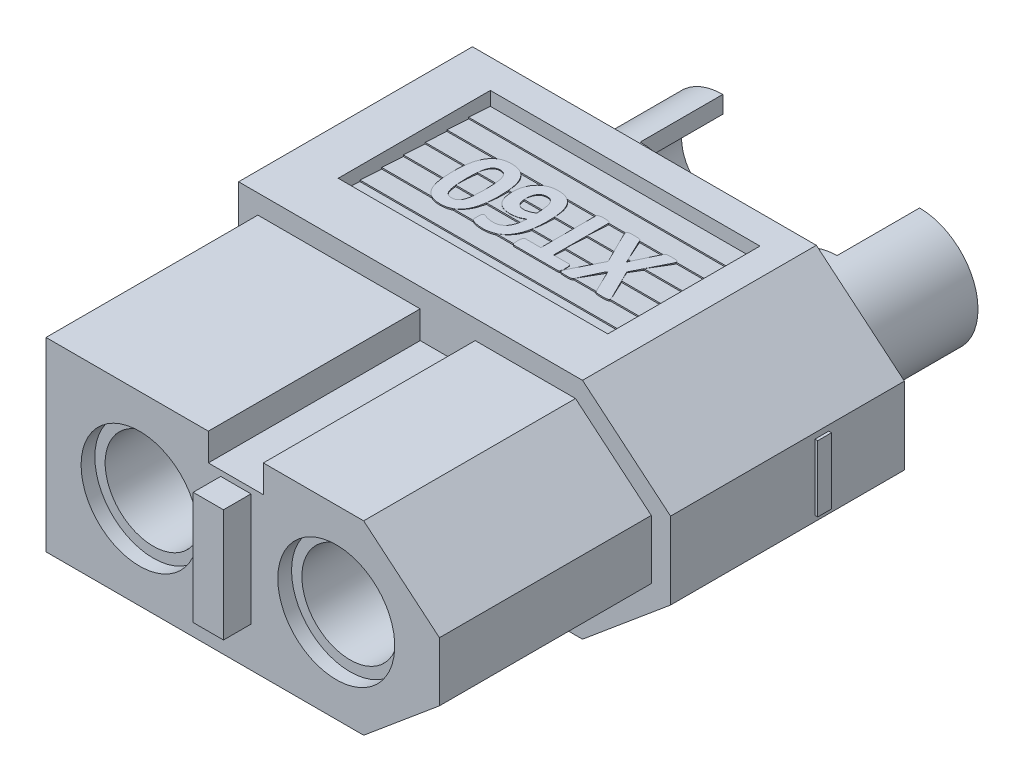
SolidWorks part; units mm, degrees
material "Náilon 101"
ref_plane "Plano frontal" through (0, 0, 0) normal (0, 0, 1) x (1, 0, 0)
ref_plane "Plano superior" through (0, 0, 0) normal (0, 1, 0) x (1, 0, 0)
ref_plane "Plano direito" through (0, 0, 0) normal (1, 0, 0) x (0, 0, -1)
sketch "Esboço1" plane through (0, 0, 0) normal (0, 0, 1) x (1, 0, 0)
  line L0 (0, 0) -> (0, 4.075)
  line L1 (0, 4.075) -> (12.5, 4.075)
  line L2 (12.5, 4.075) -> (15.7, 1.4)
  line L3 (15.7, 1.4) -> (15.7, -1.4)
  line L4 (15.7, 0) -> (0, 0) construction
  line L5 (12.5, -4.075) -> (15.7, -1.4)
  line L6 (0, -4.075) -> (12.5, -4.075)
  line L7 (0, 0) -> (0, -4.075)
  dimension "D1" = 8.15
  dimension "D2" = 12.5
  dimension "D3" = 15.7
  dimension "D4" = 2.8
extrude "Ressalto-extrusão1" add sketch "Esboço1" against normal blind 16.2
sketch "Esboço2" plane through (0, 0, 0) normal (0, 0, 1) x (1, 0, 0)
  line L12 (0.7, 3.375) -> (0.7, -3.375)
  line L13 (0.7, -3.375) -> (12.246, -3.375)
  line L14 (12.246, -3.375) -> (15, -1.0728)
  line L15 (15, -1.0728) -> (15, 1.0728)
  line L16 (15, 1.0728) -> (12.246, 3.375)
  line L17 (12.246, 3.375) -> (0.7, 3.375)
  line L18 (0.7, 3.375) -> (0.7, -3.375)
  line L19 (0.7, -3.375) -> (12.246, -3.375)
  line L20 (12.246, -3.375) -> (15, -1.0728)
  line L21 (15, -1.0728) -> (15, 1.0728)
  line L22 (15, 1.0728) -> (12.246, 3.375)
  line L23 (12.246, 3.375) -> (0.7, 3.375)
  dimension "D1" = 0.7
sketch "Esboço3" plane through (15.7, 0, 0) normal (1, 0, 0) x (0, 0, -1)
  line L0 (13.2, 0) -> (16.2, 0) construction
  line L1 (12.95, -1.2) -> (13.45, -1.2)
  line L2 (12.95, -1.2) -> (12.95, 1.2)
  line L3 (12.95, 1.2) -> (13.45, 1.2)
  line L4 (13.45, -1.2) -> (13.45, 1.2)
  line L5 (12.95, -1.2) -> (13.45, 1.2) construction
  line L6 (12.95, 1.2) -> (13.45, -1.2) construction
  line L7 (16.2, -1.4) -> (16.2, 1.4) construction
  point P0 (13.2, 0)
  dimension "D1" = 0.5
  dimension "D2" = 2.4
  dimension "D3" = 3
extrude "Ressalto-extrusão2" add sketch "Esboço3" along normal blind 0.1 and the other way offset from surface (15.8 mm away) 0.1 other way up to face at (0, 0, -8.1)
sketch "Esboço4" plane through (0, 0, 0) normal (-1, 0, 0) x (0, 0, 1)
  line L0 (-13.45, 0) -> (-12.95, 0) construction
  line L1 (-13.45, -1.2) -> (-13.45, 1.2) construction
  line L2 (-12.95, 1.2) -> (-12.95, -1.2) construction
  line L3 (-12.95, 1.2) -> (-13.45, 1.2) construction
  line L4 (-14.4, -0.25) -> (-12, -0.25)
  line L5 (-14.4, -0.25) -> (-14.4, 0.25)
  line L6 (-14.4, 0.25) -> (-12, 0.25)
  line L7 (-12, -0.25) -> (-12, 0.25)
  line L8 (-14.4, -0.25) -> (-12, 0.25) construction
  line L9 (-14.4, 0.25) -> (-12, -0.25) construction
  point P6 (-13.2, 0)
extrude "Ressalto-extrusão3" add sketch "Esboço4" along normal up to surface (0.1 mm away) up to face at (-0.1, 0, -13.2)
sketch "Esboço5" plane through (0, 0, -16.2) normal (0, 0, -1) x (-1, 0, 0)
  line L0 (-15.7, 0) -> (-11.25, 0) construction
  line L1 (-15.7, -1.4) -> (-15.7, 1.4) construction
  line L2 (-11.25, 0) -> (-4.1, 0) construction
  line L3 (-4.1, 0) -> (0, 0) construction
  line L4 (0, 0.25) -> (0, -0.25) construction
  circle A0 centre (-4.1, 0) radius 2.925
  circle A1 centre (-11.25, 0) radius 2.925
  dimension "D1" = 5.85
  dimension "D2" = 7.15
  dimension "D3" = 4.1
extrude "Corte-extrusão2" cut sketch "Esboço5" against normal blind 3.5
sketch "Esboço6" plane through (0, 0, -12.7) normal (0, 0, -1) x (-1, 0, 0)
  circle A2 centre (-11.25, 0) radius 2.125
  circle A3 centre (-4.1, 0) radius 2.125
  dimension "D1" = 4.25
extrude "Corte-extrusão3" cut sketch "Esboço6" against normal through all
sketch "Esboço7" plane through (0, 0, -16.2) normal (0, 0, -1) x (-1, 0, 0)
  circle A0 centre (-11.25, 0) radius 2.125 construction
  circle A1 centre (-4.1, 0) radius 2.125 construction
  circle A2 centre (-11.25, 0) radius 2.125
  circle A3 centre (-4.1, 0) radius 2.125
extrude "Ressalto-extrusão4" add sketch "Esboço7" along normal blind 5 and the other way offset from surface (15.7 mm away) 0.5 other way up to face at (9.125, 0, 0)
hole_wizard "Furo de diâmetro Ø3.0 (3)1" positions "Esboço9" profile "Esboço8" hole size "Ø3.0" standard "Métrico Ansi"
sketch "Esboço9" plane through (0, 0, -21.2) normal (0, 0, -1) x (-1, 0, 0)
  point P0 (-11.25, 0)
  point P1 (-4.1, 0)
sketch "Esboço8" plane through (11.25, 0, -21.2) normal (1, 0, 0) x (0, 1, 0)
  line L0 (0, 0) -> (0, 4.5013)
  line L1 (0, 4.5013) -> (1.5, 3.6)
  line L2 (1.5, 3.6) -> (1.5, 0)
  line L5 (1.5, 0) -> (0, 0)
  line L10 (0, 4.5013) -> (-1.5, 3.6) construction
  line L11 (0, -6.35) -> (0, 107.95) construction
  dimension "Hole Dia." = 3
  dimension "Hole Depth" = 3.6
  dimension "Drill Angle" = 118
sketch "Esboço10" plane through (0, 4.075, 0) normal (0, 1, 0) x (1, 0, 0)
  line L0 (4.1, 21.2) -> (11.25, 21.2) construction
  line L1 (5.6, 21.2) -> (2.6, 21.2) construction
  line L2 (13.375, 21.2) -> (9.125, 21.2) construction
  line L3 (7.675, 21.2) -> (7.675, 16.2) construction
  line L4 (12.5, 16.2) -> (0, 16.2) construction
  line L5 (6.225, 12.7) -> (6.225, 21.2) construction
  line L6 (4.1, 21.2) -> (6.225, 21.2)
  line L7 (4.1, 21.2) -> (4.1, 18.2)
  line L8 (4.1, 18.2) -> (6.225, 18.2)
  line L9 (6.225, 21.2) -> (6.225, 18.2)
  line L10 (9.125, 21.2) -> (9.125, 18.2)
  line L11 (11.25, 18.2) -> (9.125, 18.2)
  line L12 (11.25, 21.2) -> (11.25, 18.2)
  line L13 (11.25, 21.2) -> (9.125, 21.2)
  dimension "D1" = 3
extrude "Corte-extrusão4" cut sketch "Esboço10" against normal through all
sketch "Esboço12" plane through (0, 0, 0) normal (-1, 0, 0) x (0, 0, 1)
  line L0 (-15.15, 4.075) -> (-15.15, 3.575)
  line L1 (-16.2, 4.075) -> (0, 4.075) construction
  line L2 (-15.15, 3.575) -> (-14.36, 3.625)
  line L3 (-14.36, 3.625) -> (-14.36, 3.575)
  line L4 (-15.15, 3.575) -> (-9.62, 3.575) construction
  line L5 (-16.2, 4.075) -> (-16.2, -4.075) construction
  line L6 (-14.36, 3.575) -> (-13.57, 3.625)
  line L7 (-13.57, 3.625) -> (-13.57, 3.575)
  line L8 (-13.57, 3.575) -> (-12.78, 3.625)
  line L9 (-12.78, 3.625) -> (-12.78, 3.575)
  line L10 (-12.78, 3.575) -> (-11.99, 3.625)
  line L11 (-11.99, 3.625) -> (-11.99, 3.575)
  line L12 (-11.99, 3.575) -> (-11.2, 3.625)
  line L13 (-11.2, 3.625) -> (-11.2, 3.575)
  line L14 (-11.2, 3.575) -> (-10.41, 3.625)
  line L15 (-10.41, 3.625) -> (-10.41, 3.575)
  line L16 (-10.41, 3.575) -> (-9.62, 3.625)
  line L17 (-9.62, 3.625) -> (-9.62, 3.575) construction
  line L18 (-15.15, 3.575) -> (-14.36, 3.575) construction
  line L19 (-9.62, 3.625) -> (-9.62, 4.075)
  line L20 (-15.15, 4.075) -> (-9.62, 4.075)
  line L21 (-9.62, 4.075) -> (-9.6373, 4.0753)
  line M2 (0, 4.075) -> (-16.2, 4.075)
  dimension "D1" = 0.5
  dimension "D2" = 0.79
  dimension "D3" = 0.05
  dimension "D4" = 1.05
  dimension "D6" = 0.79
  dimension "D5" = 7
extrude "Corte-extrusão5" cut sketch "Esboço12" against normal blind 9.8 from offset 1.7 contours L16 L19 L0 L2 L3 L6 L7 L8 L9 L10 L11 L12 L13 L14 L15 M2 offset against normal yes
mirror "Espelhar1" about plane through (0, 0, 0) normal (0, 1, 0) of "Corte-extrusão5"
ref_plane "Plano1" through (0, 3.575, 0) normal (0, 1, 0) x (-1, 0, 0)
sketch "Esboço13" plane through (0, 3.575, 0) normal (0, 1, 0) x (-1, 0, 0)
  line L0 (-10.1, -13.635) -> (-3.1, -13.635) construction
  line L1 (-3.1, -13.635) -> (-6.6, -13.635) construction
  line L2 (-6.6, -13.635) -> (-6.6, -15.15) construction
  line L4 (-11.5, -15.15) -> (-1.7, -15.15) construction
  line L5 (-10.1, -13.635) -> (-10.1, -11.135) construction
  line L6 (-10.1, -11.135) -> (-3.1, -11.135) construction
  line L7 (-3.1, -11.135) -> (-3.1, -13.635) construction
  line L8 (-6.6, -11.135) -> (-6.6, -9.62) construction
  line L9 (-11.5, -9.62) -> (-1.7, -9.62) construction
  text T0 "XT60" font "Calibri" height 2.5
  dimension "D1" = 7
  dimension "D2" = 2.5
extrude "Ressalto-extrusão6" add sketch "Esboço13" along normal up to vertex (0.05 mm away) up to point (11.5, 3.625, -11.2)
ref_plane "Plano2" through (0, -3.575, 0) normal (0, 1, 0) x (-1, 0, 0)
sketch "Esboço14" plane through (0, -3.575, 0) normal (0, 1, 0) x (-1, 0, 0)
  line L0 (-6.6, -9.62) -> (-6.6, -10.735) construction
  line L1 (-11.5, -9.62) -> (-1.7, -9.62) construction
  line L2 (-6.6, -10.735) -> (-2.8, -10.735) construction
  line L3 (-2.8, -10.735) -> (-2.8, -14.035) construction
  line L4 (-2.8, -14.035) -> (-10.4, -14.035) construction
  line L5 (-10.4, -14.035) -> (-10.4, -10.735) construction
  line L6 (-10.4, -10.735) -> (-6.6, -10.735) construction
  line L7 (-6.6, -14.035) -> (-6.6, -15.15) construction
  line L8 (-11.5, -15.15) -> (-1.7, -15.15) construction
  text T0 "TGY" font "Calibri" height 3.3
  dimension "D1" = 3.3
  dimension "D2" = 7.6
extrude "Ressalto-extrusão7" add sketch "Esboço14" against normal up to vertex (0.05 mm away) up to point (1.7, -3.625, -10.41)
extrude "Corte-extrusão7" cut sketch "Esboço2" against normal blind 7.7 flip side to cut
sketch "Esboço16" plane through (0, 0, 0) normal (0, 0, 1) x (1, 0, 0)
  line L0 (12.246, 3.375) -> (0.7, 3.375) construction
  line L1 (6.6, 3.375) -> (8.6, 3.375)
  line L2 (6.6, 3.375) -> (6.6, 2.375)
  line L3 (6.6, 2.375) -> (8.6, 2.375)
  line L4 (8.6, 3.375) -> (8.6, 2.375)
  line L5 (0.7, 3.375) -> (0.7, -3.375) construction
  dimension "D1" = 5.9
  dimension "D2" = 2
  dimension "D3" = 1
extrude "Corte-extrusão8" cut sketch "Esboço16" against normal up to surface (7.7 mm away) up to face at (9.4, 0, -7.7)
sketch "Esboço17" plane through (0, 0, 0) normal (0, 0, 1) x (1, 0, 0)
  line L0 (7.6, 2.375) -> (7.6, 0.125) construction
  line L1 (7.05, -1.925) -> (8.15, -1.925)
  line L2 (7.05, -1.925) -> (7.05, 2.175)
  line L3 (7.05, 2.175) -> (8.15, 2.175)
  line L4 (8.15, -1.925) -> (8.15, 2.175)
  line L5 (7.05, -1.925) -> (8.15, 2.175) construction
  line L6 (7.05, 2.175) -> (8.15, -1.925) construction
  line L7 (8.6, 2.375) -> (6.6, 2.375) construction
  point P0 (7.6, 0.125)
  dimension "D1" = 1.1
  dimension "D2" = 4.1
  dimension "D3" = 0.2
extrude "Ressalto-extrusão8" add sketch "Esboço17" along normal blind 1
hole_wizard "Furo de diâmetro Ø3.5 (3.5)1" positions "Esboço19" profile "Esboço18" hole size "Ø3.5" standard "Métrico Ansi"
sketch "Esboço19" plane through (0, 0, -0.5) normal (0, 0, 1) x (1, 0, 0)
  point P0 (4.1, 0)
  point P1 (11.25, 0)
sketch "Esboço18" plane through (4.1, 0, -0.5) normal (1, 0, 0) x (0, -1, 0)
  line L0 (0, 0) -> (0, 13.0515)
  line L1 (0, 13.0515) -> (1.75, 12)
  line L2 (1.75, 12) -> (1.75, 0)
  line L5 (1.75, 0) -> (0, 0)
  line L10 (0, 13.0515) -> (-1.75, 12) construction
  line L11 (0, -6.35) -> (0, 107.95) construction
  dimension "Hole Dia." = 3.5
  dimension "Hole Depth" = 12
  dimension "Drill Angle" = 118
